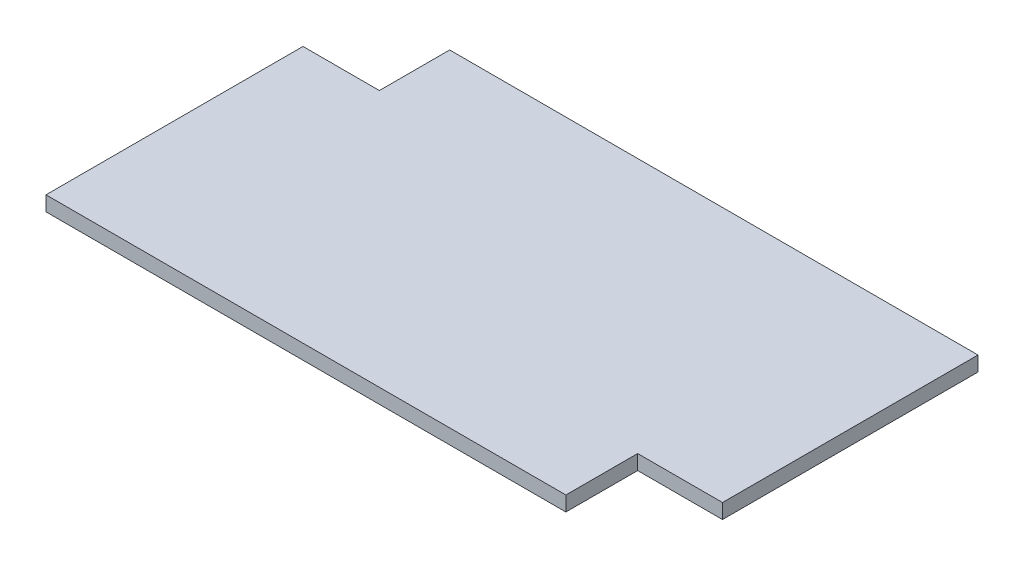
SolidWorks part; units mm, degrees
ref_plane "Front Plane" through (0, 0, 0) normal (0, 0, 1) x (1, 0, 0)
ref_plane "Top Plane" through (0, 0, 0) normal (0, 1, 0) x (1, 0, 0)
ref_plane "Right Plane" through (0, 0, 0) normal (1, 0, 0) x (0, 0, -1)
sketch "Sketch1" plane through (0, 0, 0) normal (0, 1, 0) x (1, 0, 0)
  line L0 (45.3312, -48.9002) -> (45.3312, -34.3263)
  line L5 (62.5573, 17.5518) -> (-44.7186, 17.5518)
  line L6 (62.5573, 17.5518) -> (62.5573, -34.3263)
  line L7 (45.3312, -48.9002) -> (-60.2273, -48.9002)
  line L8 (-60.2273, 3.2809) -> (-60.2273, -48.9002)
  line L9 (45.3312, -34.3263) -> (62.5573, -34.3263)
  line L10 (-60.2273, 3.2809) -> (-44.7186, 3.2809)
  line L11 (-44.7186, 3.2809) -> (-44.7186, 17.5518)
  point P0 (0, 0)
  point P3 (-45.3185, -1.2948)
  point P4 (-60.4711, -1.2948)
  point P9 (-60.4713, -1.0572)
  point P13 (-59.3093, -50.345)
  point P14 (-45.4565, -1.0893)
  point P15 (-60.3438, -1.1395)
  point P16 (44.7764, -39.3631)
  point P17 (45.0521, -39.2902)
  point P18 (-44.8975, 16.7835)
  point P19 (-45.1966, 17.5518)
  point P20 (45.2411, -35.9842)
  point P21 (45.5445, -36.217)
  point P22 (62.5573, -36.2391)
  point P23 (-60.3438, -49.018)
  point P24 (-60.2273, -48.9002)
  point P25 (45.5337, -34.6231)
  point P26 (0, 0)
  point P27 (45.3312, -34.3263)
  point P28 (-42.7205, 2.6608)
  point P29 (-44.7186, 3.2809)
extrude "Boss-Extrude1" add sketch "Sketch1" along normal blind 3
